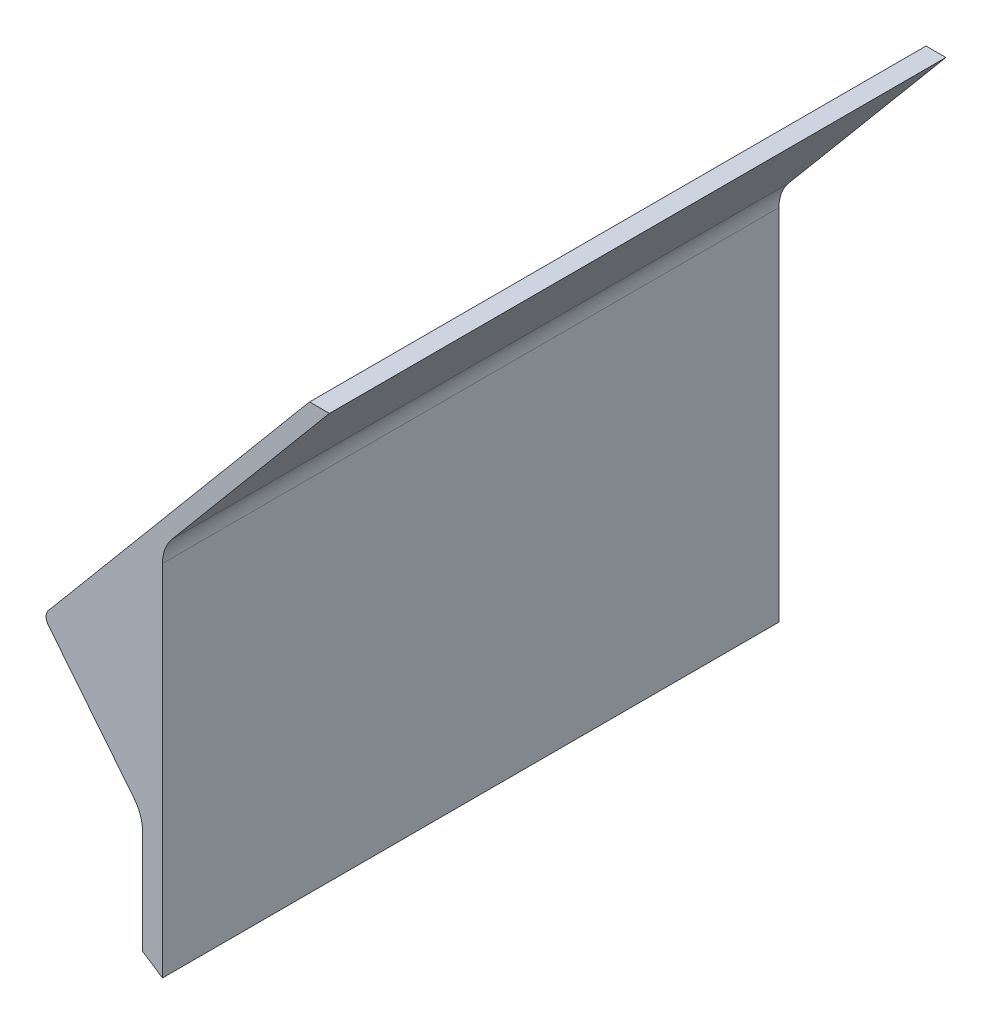
SolidWorks part; units mm, degrees
material "201 Annealed Stainless Steel (SS)"
ref_plane "Front Plane" through (0, 0, 0) normal (0, 0, 1) x (1, 0, 0)
ref_plane "Top Plane" through (0, 0, 0) normal (0, 1, 0) x (1, 0, 0)
ref_plane "Right Plane" through (0, 0, 0) normal (1, 0, 0) x (0, 0, -1)
sketch "Sketch1" plane through (0, 0, 0) normal (0, 0, 1) x (1, 0, 0)
  line L0 (0, 0) -> (0, 93.9)
  line L1 (0, 93.9) -> (41.974, 143.9227)
  line L2 (41.974, 143.9227) -> (36.974, 143.9227)
  line L3 (36.974, 143.9227) -> (-30, 64.1062)
  line L4 (-30, 64.1062) -> (-5, 32.8812)
  line L5 (-5, 32.8812) -> (-5, 3.2669)
  line L7 (-5, 0) -> (-45, 0) construction
  line L8 (-30, 0) -> (-30, 91.2241) construction
  line L9 (-5, 0) -> (-5, -132.2876) construction
  line L10 (-5, -132.2876) -> (-90, -132.2876) construction
  circle A0 centre (-90, -132.2876) radius 160 construction
  arc A1 (0, 0) -> (-5, 3.2669) centre (-90, -132.2876) ccw
  dimension "D9" = 320
  dimension "D1" = 5
  dimension "D2" = 5
  dimension "D3" = 140
  dimension "D4" = 65.3
  dimension "D5" = 93.9
  dimension "D6" = 40
  dimension "D7" = 25
  dimension "D8" = 40
  dimension "D10" = 85
extrude "Funnel - Right Side" add sketch "Sketch1" along normal blind 155
fillet "Fillet2" radius 10 2 edges at (0, 93.9, 77.5) (-5, 32.8812, 77.5)
fillet "Fillet3" radius 2.5 1 edges at (-30, 64.1062, 77.5)
